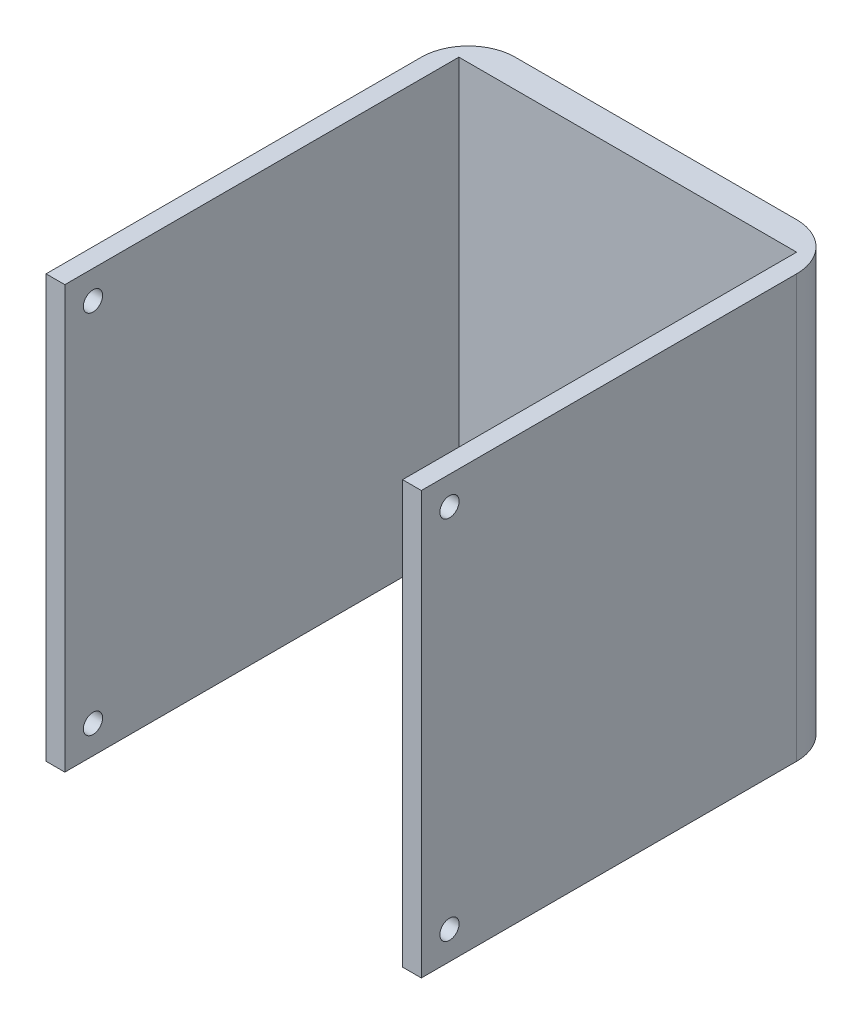
SolidWorks part; units mm, degrees
ref_plane "前基準面" through (0, 0, 0) normal (0, 0, 1) x (1, 0, 0)
ref_plane "上基準面" through (0, 0, 0) normal (0, 1, 0) x (1, 0, 0)
ref_plane "右基準面" through (0, 0, 0) normal (1, 0, 0) x (0, 0, -1)
sketch "草圖1" plane through (0, 0, 0) normal (0, 0, 1) x (1, 0, 0)
  line L1 (-14.5455, 16.9091) -> (25.4545, 16.9091)
  line L2 (-14.5455, 16.9091) -> (-14.5455, -28.0909)
  line L3 (-14.5455, -28.0909) -> (25.4545, -28.0909)
  line L4 (25.4545, 16.9091) -> (25.4545, -28.0909)
  dimension "D1" = 40
  dimension "D2" = 45
extrude "填料-伸長1" add sketch "草圖1" along normal blind 40 and the other way blind 5 contours L4 L3 L2 L1
sketch "草圖2" plane through (0, 16.9091, 0) normal (0, 1, 0) x (1, 0, 0)
  line L0 (5.4545, 5) -> (5.4545, -40.6532) construction
  line L1 (-14.5455, 5) -> (25.4545, 5) construction
  line L2 (-14.5455, -40) -> (25.4545, -40) construction
  line L3 (-12.5455, -3) -> (23.4545, -3)
  line L4 (-12.5455, -3) -> (-12.5455, -40)
  line L5 (-12.5455, -40) -> (23.4545, -40)
  line L6 (23.4545, -3) -> (23.4545, -40)
  line L7 (-14.5455, -40) -> (-14.5455, 5) construction
  line L8 (25.4545, -40) -> (25.4545, 5) construction
  dimension "D1" = 2
  dimension "D2" = 2
  dimension "D3" = 37
extrude "除料-伸長1" cut sketch "草圖2" against normal blind 50
sketch "草圖3" plane through (-14.5455, 0, 0) normal (-1, 0, 0) x (0, 0, 1)
  line L1 (40, -28.0909) -> (-5, -28.0909) construction
  line L2 (40, 16.9091) -> (40, -28.0909) construction
  line L3 (40, 16.9091) -> (-5, 16.9091) construction
  circle A1 centre (37, -25.0909) radius 1.025
  circle A2 centre (37, 13.9091) radius 1.025
  dimension "D5" = 3
  dimension "D6" = 2.05
  dimension "D1" = 2.05
  dimension "D2" = 3
  dimension "D3" = 3
  dimension "D4" = 3
extrude "除料-伸長2" cut sketch "草圖3" against normal blind 2
sketch "草圖4" plane through (25.4545, 0, 0) normal (1, 0, 0) x (0, 0, -1)
  line L0 (-40, 16.9091) -> (-40, -28.0909) construction
  line L1 (-40, -28.0909) -> (5, -28.0909) construction
  line L2 (-40, 16.9091) -> (5, 16.9091) construction
  circle A0 centre (-37, 13.9091) radius 1.025
  circle A1 centre (-37, -25.0909) radius 1.025
  dimension "D1" = 2.05
  dimension "D2" = 2.05
  dimension "D3" = 3
  dimension "D4" = 3
  dimension "D5" = 3
  dimension "D6" = 3
extrude "除料-伸長3" cut sketch "草圖4" against normal blind 2
sketch "草圖5" plane through (0, 16.9091, 0) normal (0, 1, 0) x (1, 0, 0)
  line L1 (-12.5455, -3) -> (23.4545, -3)
  line L2 (-12.5455, -3) -> (-12.5455, 2)
  line L3 (-12.5455, 2) -> (23.4545, 2)
  line L4 (23.4545, -3) -> (23.4545, 2)
  dimension "D1" = 36
  dimension "D2" = 5
extrude "除料-伸長4" cut sketch "草圖5" against normal blind 43
fillet "圓角6" radius 5 1 edges at (-14.5455, -5.5909, -5)
fillet "圓角7" radius 5 1 edges at (25.4545, -5.5909, -5)
